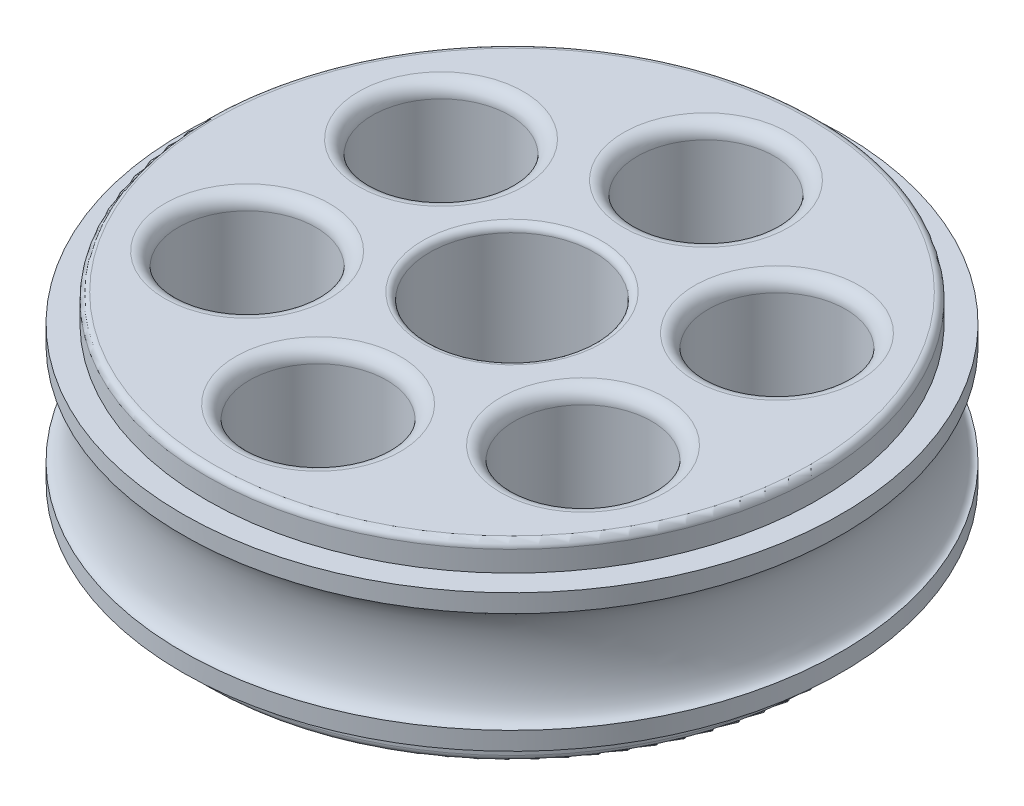
SolidWorks part; units mm, degrees
ref_plane "Front" through (0, 0, 0) normal (0, 0, 1) x (1, 0, 0)
ref_plane "Top" through (0, 0, 0) normal (0, 1, 0) x (1, 0, 0)
ref_plane "Right" through (0, 0, 0) normal (1, 0, 0) x (0, 0, -1)
sketch "Sketch1" plane through (0, 0, 0) normal (0, 1, 0) x (1, 0, 0)
  circle A0 centre (0, 0) radius 28.2575
  dimension "D1" = 56.515
extrude "Step" add sketch "Sketch1" along normal blind 2.54
sketch "Sketch2" plane through (0, 2.54, 0) normal (0, 1, 0) x (1, 0, 0)
  circle A0 centre (0, 0) radius 30.48
  dimension "D1" = 60.96
extrude "Body" add sketch "Sketch2" along normal blind 12.7
sketch "Sketch3" plane through (0, 15.24, 0) normal (0, 1, 0) x (1, 0, 0)
  circle A0 centre (0, 0) radius 28.2575
  dimension "D1" = 56.515
extrude "Mirror_Step" add sketch "Sketch3" along normal blind 2.54
sketch "Sketch4" plane through (0, 17.78, 0) normal (0, 1, 0) x (1, 0, 0)
  circle A0 centre (0, 0) radius 7.62
  dimension "D1" = 15.24
extrude "Cut-Extrude1" cut sketch "Sketch4" against normal through all
fillet "Fillet1" radius 0.635 4 edges at (0, 17.78, 28.2575) (0, 0, 28.2575) (0, 0, 7.62) (0, 17.78, 7.62)
sketch "Sketch5" plane through (0, 0, 0) normal (0, -1, 0) x (1, 0, 0)
  line L0 (0, 11.5887) -> (0, 8.255) construction
  line L1 (0, 24.2887) -> (0, 27.6225) construction
  circle A0 centre (0, 17.9387) radius 6.35
  circle A1 centre (0, 0) radius 8.255 construction
  circle A2 centre (0, 0) radius 27.6225 construction
  circle A3 centre (15.5354, 8.9694) radius 6.35
  circle A4 centre (15.5354, -8.9694) radius 6.35
  circle A5 centre (0, -17.9387) radius 6.35
  circle A6 centre (-15.5354, -8.9694) radius 6.35
  circle A7 centre (-15.5354, 8.9694) radius 6.35
  point P24 (0, 0)
  dimension "D1" = 12.7
  dimension "D2" = 6
extrude "Cut-Extrude2" cut sketch "Sketch5" against normal through all
fillet "Fillet2" radius 1.27 12 edges at (0, 0, 11.5887) (0, 17.78, 11.5887) (-15.5354, 0, 2.6194) (-15.5354, 17.78, 2.6194) (-15.5354, 0, -15.3194) (-15.5354, 17.78, -15.3194) (0, 0, -24.2888) (0, 17.78, -24.2888) (15.5354, 0, -15.3194) (15.5354, 17.78, -15.3194) (15.5354, 0, 2.6194) (15.5354, 17.78, 2.6194)
sketch "Sketch6" plane through (0, 0, 0) normal (1, 0, 0) x (0, 0, -1)
  line L0 (-30.48, 2.54) -> (30.48, 2.54) construction
  line L1 (30.48, 15.24) -> (-30.48, 15.24) construction
  line L2 (-30.48, 2.54) -> (30.48, 2.54) construction
  line L3 (30.48, 15.24) -> (-30.48, 15.24) construction
  line L4 (-30.48, 2.54) -> (-30.48, 15.24) construction
  line L5 (0, 2.54) -> (0, 15.24) construction
  ellipse E0 centre (-30.48, 8.89) end of major axis (-30.48, 13.5622) minor radius 1.6186
revolve "Groove" cut sketch "Sketch6" angle 360 about L5
